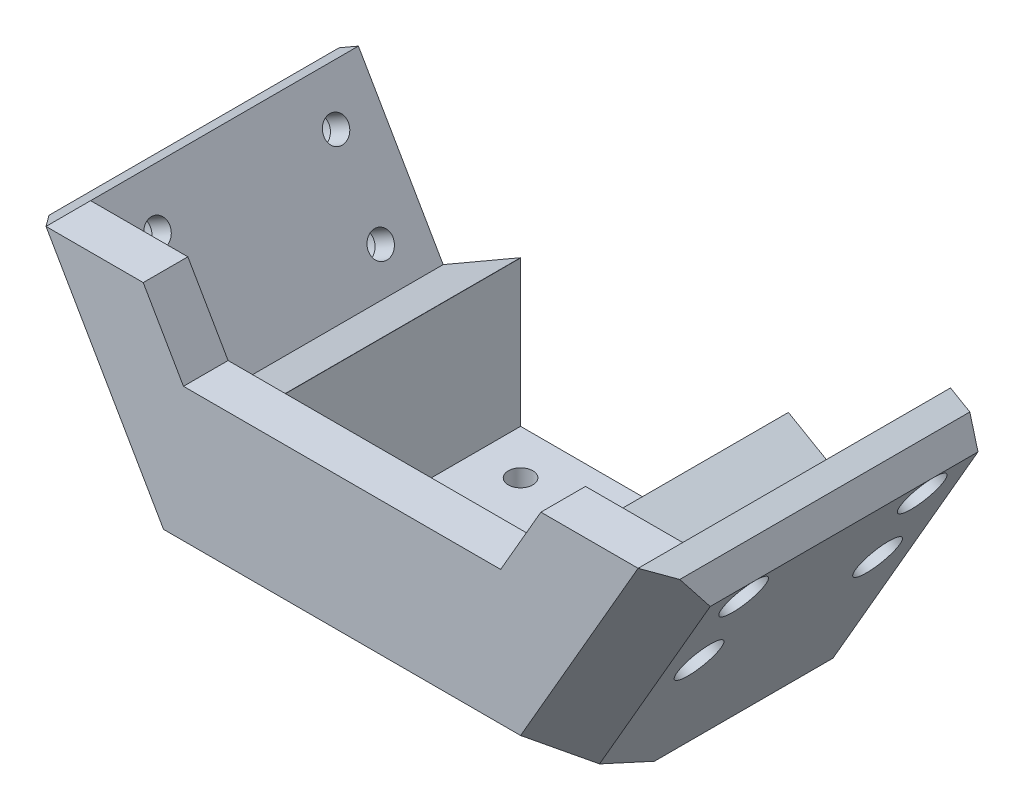
SolidWorks part; units mm, degrees
ref_plane "Front Plane" through (0, 0, 0) normal (0, 0, 1) x (1, 0, 0)
ref_plane "Top Plane" through (0, 0, 0) normal (0, 1, 0) x (1, 0, 0)
ref_plane "Right Plane" through (0, 0, 0) normal (1, 0, 0) x (0, 0, -1)
sketch "Sketch1" plane through (0, 0, 0) normal (0, 0, 1) x (1, 0, 0)
  line L0 (0, 0) -> (0, 48.2132) construction
  line L5 (-40, -20) -> (-75, 40.6218)
  line L6 (-75, 40.6218) -> (-40.359, 60.6218)
  line L7 (-40.359, 60.6218) -> (-22.6795, 30)
  line L15 (40, -20) -> (75, 40.6218)
  line L16 (-40, -20) -> (40, -20)
  line L18 (-22.6795, 30) -> (22.6795, 30)
  line L20 (-40, -20) -> (0, 0) construction
  line L21 (0, 0) -> (40, -20) construction
  line L22 (75, 40.6218) -> (40.359, 60.6218)
  line L23 (40.359, 60.6218) -> (22.6795, 30)
  point P0 (0, 0)
  dimension "D1" = 60
  dimension "D2" = 50
  dimension "D6" = 80
  dimension "D8" = 70
  dimension "D9" = 40
extrude "Boss-Extrude1" add sketch "Sketch1" along normal blind 70
sketch "Sketch2" plane through (0, 0, 0) normal (0, 0, -1) x (-1, 0, 0)
  line L0 (66.3397, 45.6218) -> (47.3397, 12.7128)
  line L7 (66.3397, 45.6218) -> (49.0192, 55.6218)
  line L8 (49.0192, 55.6218) -> (30.0192, 22.7128)
  line L9 (47.3397, 12.7128) -> (30.0192, 22.7128)
  line L10 (66.3397, 45.6218) -> (30.0192, 22.7128) construction
  line L11 (49.0192, 55.6218) -> (47.3397, 12.7128) construction
  line L12 (75, 40.6218) -> (40, -20) construction
  line L14 (40.359, 60.6218) -> (75, 40.6218) construction
  line L15 (0, 0) -> (0, 54.4531) construction
  line L16 (-49.0192, 55.6218) -> (-47.3397, 12.7128) construction
  line L17 (-66.3397, 45.6218) -> (-30.0192, 22.7128) construction
  line L18 (-47.3397, 12.7128) -> (-30.0192, 22.7128)
  line L19 (-49.0192, 55.6218) -> (-30.0192, 22.7128)
  line L20 (-66.3397, 45.6218) -> (-49.0192, 55.6218)
  line L21 (-66.3397, 45.6218) -> (-47.3397, 12.7128)
  point P0 (0, 0)
  point P6 (48.1795, 34.1673)
  point P21 (-48.1795, 34.1673)
  dimension "D1" = 20
  dimension "D3" = 38
  dimension "D4" = 20
  dimension "D5" = 10
extrude "Cut-Extrude1" cut sketch "Sketch2" against normal blind 60
chamfer "Chamfer2" distance 30 distance2 20 1 edges at (0, -20, 70)
sketch "Sketch4" plane through (0, 0, 0) normal (0, 0, -1) x (-1, 0, 0)
  line L1 (-30, -10) -> (30, -10)
  line L2 (-30, -10) -> (-30, 10)
  line L3 (-30, 10) -> (30, 10)
  line L4 (30, -10) -> (30, 10)
  line L5 (-30, -10) -> (30, 10) construction
  line L6 (-30, 10) -> (30, -10) construction
  line L8 (40, -20) -> (-40, -20) construction
  point P0 (0, 0)
  dimension "D1" = 20
  dimension "D2" = 60
  dimension "D3" = 10
extrude "Cut-Extrude3" cut sketch "Sketch4" against normal blind 40
sketch "Sketch5" plane through (0, 0, 0) normal (0, 0, -1) x (-1, 0, 0)
  line L0 (30, 10) -> (30, 22.6795)
  line L1 (30, 22.6795) -> (49.0192, 55.6218)
  line L2 (49.0192, 55.6218) -> (40.359, 60.6218)
  line L3 (40.359, 60.6218) -> (-40.359, 60.6218)
  line L4 (-40.359, 60.6218) -> (-49.0192, 55.6218)
  line L5 (-49.0192, 55.6218) -> (-30, 22.6795)
  line L6 (-30, 22.6795) -> (-30, 10)
  line L7 (30, 10) -> (-30, 10) construction
  line L8 (30, 10) -> (-30, 10) construction
  line L9 (-30, 10) -> (30, 10)
extrude "Cut-Extrude4" cut sketch "Sketch5" against normal blind 60
sketch "Sketch7" plane through (0, 0, 70) normal (0, 0, 1) x (1, 0, 0)
  line L0 (66.3397, 45.6218) -> (44.5534, 45.6218)
  line L1 (-66.3397, 45.6218) -> (-40.359, 60.6218)
  line L2 (-40.359, 60.6218) -> (40.359, 60.6218)
  line L3 (40.359, 60.6218) -> (66.3397, 45.6218)
  line L4 (35.5342, 30) -> (44.5534, 45.6218)
  line L5 (-35.5342, 30) -> (-44.5534, 45.6218)
  line L10 (-44.5534, 45.6218) -> (-66.3397, 45.6218)
  line L11 (-35.5342, 30) -> (35.5342, 30)
extrude "Cut-Extrude7" cut sketch "Sketch7" against normal blind 60
chamfer "Chamfer5" distance 5 angle 45 2 edges at (-75, 40.6218, 35) (75, 40.6218, 35)
sketch "Sketch8" plane through (0, -20, 0) normal (0, -1, 0) x (1, 0, 0)
  line L0 (-40, 0) -> (40, 0) construction
  line L1 (0, 0) -> (0, 52.0616) construction
  circle A0 centre (20, 10) radius 2.75
  circle A1 centre (20, 30) radius 2.75
  circle A2 centre (-20, 30) radius 2.75
  circle A3 centre (-20, 10) radius 2.75
  dimension "D1" = 5.5
  dimension "D2" = 20
  dimension "D3" = 20
  dimension "D4" = 10
  dimension "D5" = 30
extrude "Cut-Extrude8" cut sketch "Sketch8" against normal through all
sketch "Sketch9" plane through (38.6603, -22.3205, 0) normal (0.866, -0.5, 0) x (0, 0, -1)
  line L0 (0, 2.6795) -> (0, 67.6795) construction
  line L2 (-30, 72.6795) -> (-30, 42.126) construction
  line L3 (-70, 72.6795) -> (0, 72.6795) construction
  circle A0 centre (-10, 62.6795) radius 2.75
  circle A1 centre (-10, 42.6795) radius 2.75
  circle A2 centre (-50, 42.6795) radius 2.75
  circle A3 centre (-50, 62.6795) radius 2.75
  dimension "D1" = 5.5
  dimension "D2" = 10
  dimension "D3" = 10
  dimension "D4" = 20
  dimension "D5" = 10
  dimension "D6" = 30
extrude "Cut-Extrude9" cut sketch "Sketch9" against normal through all
mirror "Mirror1" about plane through (0, 0, 0) normal (1, 0, 0) of "Cut-Extrude9"
sketch "Sketch10" plane through (0, -20, 0) normal (0, -1, 0) x (1, 0, 0)
  circle A0 centre (20, 10) radius 5
  circle A1 centre (20, 30) radius 5
  circle A2 centre (-20, 30) radius 5
  circle A3 centre (-20, 10) radius 5
  dimension "D1" = 10
extrude "Cut-Extrude10" cut sketch "Sketch10" against normal blind 5
sketch "Sketch11" plane through (38.6603, -22.3205, 0) normal (0.866, -0.5, 0) x (0, 0, -1)
  circle A0 centre (-10, 42.6795) radius 5
  circle A1 centre (-10, 62.6795) radius 5
  circle A2 centre (-50, 62.6795) radius 5
  circle A3 centre (-50, 42.6795) radius 5
  dimension "D1" = 10
extrude "Cut-Extrude11" cut sketch "Sketch11" against normal blind 5
mirror "Mirror2" about plane through (0, 0, 0) normal (1, 0, 0) of "Cut-Extrude11"
chamfer "Chamfer6" distance 10 angle 45 2 edges at (62.0235, 18.1458, 70) (-62.0235, 18.1458, 70)
